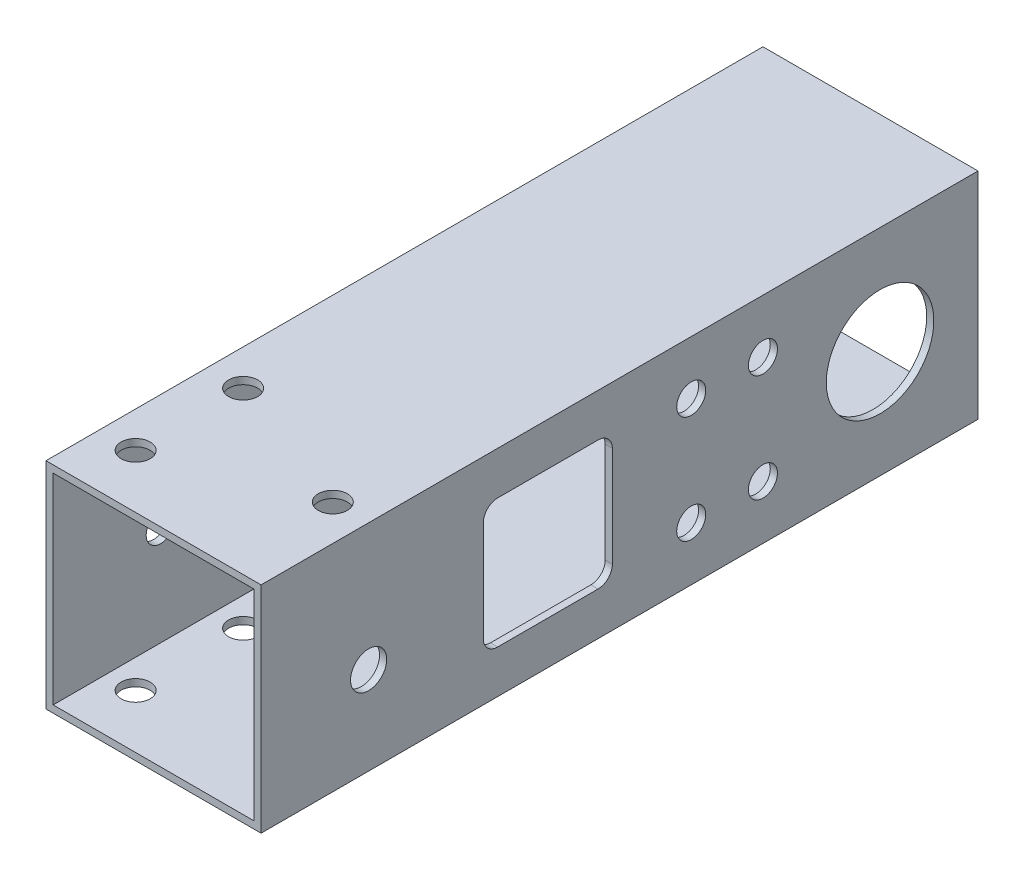
SolidWorks part; units mm, degrees
material "6063-T5"
ref_plane "前视基准面" through (0, 0, 0) normal (0, 0, 1) x (1, 0, 0)
ref_plane "上视基准面" through (0, 0, 0) normal (0, 1, 0) x (1, 0, 0)
ref_plane "右视基准面" through (0, 0, 0) normal (1, 0, 0) x (0, 0, -1)
other "Configuration Table"
sketch "草图1" plane through (0, 0, 0) normal (0, 0, 1) x (1, 0, 0)
  line L1 (-15, -15) -> (15, -15)
  line L2 (-15, -15) -> (-15, 15)
  line L3 (-15, 15) -> (15, 15)
  line L4 (15, -15) -> (15, 15)
  line L5 (-15, -15) -> (15, 15) construction
  line L6 (-15, 15) -> (15, -15) construction
  point P0 (0, 0)
  dimension "D1" = 30
extrude "凸台-拉伸1" add sketch "草图1" along normal mid plane 100
sketch "草图2" plane through (0, 0, 50) normal (0, 0, 1) x (1, 0, 0)
  line L12 (14, -14) -> (14, 14)
  line L13 (14, 14) -> (-14, 14)
  line L14 (-14, 14) -> (-14, -14)
  line L15 (-14, -14) -> (14, -14)
  line L16 (14, -14) -> (14, 14)
  line L17 (14, 14) -> (-14, 14)
  line L18 (-14, 14) -> (-14, -14)
  line L19 (-14, -14) -> (14, -14)
  dimension "D1" = 1
extrude "切除-拉伸1" cut sketch "草图2" against normal through all both and the other way through all
sketch "草图3" plane through (-15, 0, 0) normal (-1, 0, 0) x (0, 0, 1)
  circle A0 centre (10, 0) radius 2.025
  circle A1 centre (35, 0) radius 2.025
  dimension "D1" = 4.05
extrude "切除-拉伸2" cut sketch "草图3" against normal up to surface (1 mm away) up to face at (-14, 0, 0)
sketch "草图4" plane through (14, 0, 0) normal (-1, 0, 0) x (0, 0, 1)
  line L0 (50, 15) -> (-50, 15) construction
  line L1 (26, -9) -> (44, -9) construction
  line L2 (26, -9) -> (26, 9) construction
  line L3 (26, 9) -> (44, 9) construction
  line L4 (44, -9) -> (44, 9) construction
  line L5 (26, -9) -> (44, 9) construction
  line L6 (26, 9) -> (44, -9) construction
  line L7 (1, -9) -> (19, -9)
  line L8 (1, -9) -> (1, 9)
  line L9 (1, 9) -> (19, 9)
  line L10 (19, -9) -> (19, 9)
  line L11 (1, -9) -> (19, 9) construction
  line L12 (1, 9) -> (19, -9) construction
  point P0 (35, 0)
  point P6 (10, 0)
  dimension "D1" = 6
  dimension "D2" = 18
extrude "切除-拉伸3" cut sketch "草图4" against normal up to surface (1 mm away) up to face at (15, 0, 0)
fillet "圆角1" radius 2 4 edges at (14.5, -9, 1) (14.5, 9, 19) (14.5, -9, 19) (14.5, 9, 1)
sketch "草图5" plane through (0, -14, 0) normal (0, 1, 0) x (1, 0, 0)
  line L4 (15, 50) -> (-15, 50)
  line L5 (-15, 50) -> (-15, -50)
  line L6 (-15, -50) -> (15, -50)
  line L7 (15, -50) -> (15, 50)
  line L8 (15, 50) -> (-15, 50)
  line L9 (-15, 50) -> (-15, -50)
  line L10 (-15, -50) -> (15, -50)
  line L11 (15, -50) -> (15, 50)
  circle A0 centre (-10, -42.5) radius 2.025
  circle A1 centre (-10, -27.5) radius 2.025
  dimension "D2" = 4.05
  dimension "D3" = 15
  dimension "D4" = 7.5
  dimension "D5" = 5
  dimension "D1" = 0
extrude "切除-拉伸5" cut sketch "草图5" against normal through all both and the other way through all contours A1 | A0
mirror "镜向1" about plane through (0, 0, 0) normal (1, 0, 0) of "切除-拉伸5"
sketch "草图6" plane through (-15, 0, 0) normal (-1, 0, 0) x (0, 0, 1)
  line L0 (50, 15) -> (-50, 15) construction
  line L1 (50, 15) -> (50, -15) construction
  circle A0 centre (35, 0) radius 2.025
  circle A1 centre (-20, -7.5) radius 2.025
  circle A2 centre (-20, 7.5) radius 2.025
  dimension "D1" = 4.05
  dimension "D2" = 7.5
  dimension "D3" = 15
  dimension "D4" = 70
  dimension "D5" = 15
  dimension "D6" = 35
extrude "切除-拉伸6" cut sketch "草图6" against normal through all both and the other way through all
sketch "草图7" plane through (-15, 0, 0) normal (-1, 0, 0) x (0, 0, 1)
  line L0 (50, -15) -> (-50, -15) construction
  line L1 (-50, 15) -> (-50, -15) construction
  circle A0 centre (-36.3415, 0) radius 7.5
  dimension "D1" = 15
  dimension "D3" = 13.6585
  dimension "D2" = 15
extrude "切除-拉伸7" cut sketch "草图7" against normal through all both
sketch "草图8" plane through (-15, 0, 0) normal (-1, 0, 0) x (0, 0, 1)
  line L0 (-20, 7.5) -> (-10, 7.5) construction
  line L1 (-20, -7.5) -> (-10, -7.5) construction
  circle A0 centre (-10, 7.5) radius 2.025
  circle A1 centre (-10, -7.5) radius 2.025
  circle A2 centre (-20, 7.5) radius 2.025 construction
  dimension "D1" = 4.05
  dimension "D2" = 10
extrude "切除-拉伸8" cut sketch "草图8" against normal through all both and the other way through all
sketch "草图9" plane through (0, 15, 0) normal (0, 1, 0) x (1, 0, 0)
  circle A0 centre (10, -27.5) radius 2.25
  circle A1 centre (10, -42.5) radius 2.25
  dimension "D1" = 4.5
extrude "凸台-拉伸2" add sketch "草图9" against normal up to surface (1 mm away) up to face at (10, 14, 29.525)
sketch "草图10" plane through (0, -15, 0) normal (0, -1, 0) x (1, 0, 0)
  circle A0 centre (10, 42.5) radius 2.5
  circle A1 centre (10, 27.5) radius 2.5
  point P5 (10, 27.5)
  dimension "D1" = 5
extrude "凸台-拉伸3" add sketch "草图10" against normal up to surface (1 mm away) up to face at (10, -14, 25.475)
sketch "草图11" plane through (0, 15, 0) normal (0, 1, 0) x (1, 0, 0)
  line L0 (15, -50) -> (15, 50) construction
  line L1 (-10, -27.5) -> (-10, -42.5) construction
  circle A0 centre (10, -35) radius 2.025
  point P8 (-10, -35)
  dimension "D1" = 5
  dimension "D2" = 4.05
extrude "切除-拉伸9" cut sketch "草图11" against normal through all both and the other way through all
sketch "草图12" plane through (15, 0, 0) normal (1, 0, 0) x (0, 0, -1)
  circle A0 centre (-35, 0) radius 2.5
  dimension "D1" = 5
extrude "凸台-拉伸4" add sketch "草图12" against normal up to surface (1 mm away) up to face at (14, 7.5, -12.025)
sketch "草图13" plane through (15, 0, 0) normal (1, 0, 0) x (0, 0, -1)
  line L0 (-50, -15) -> (-50, 15) construction
  line L1 (-50, -15) -> (50, -15) construction
  line L2 (-50, 15) -> (50, 15) construction
  circle A0 centre (-35, 2.75) radius 2.525 construction
  circle A1 centre (-35, -2.75) radius 2.525
  point P10 (0, 0)
  dimension "D2" = 12.25
  dimension "D3" = 12.25
  dimension "D4" = 5.05
  dimension "D1" = 15
extrude "切除-拉伸10" cut sketch "草图13" against normal up to next
